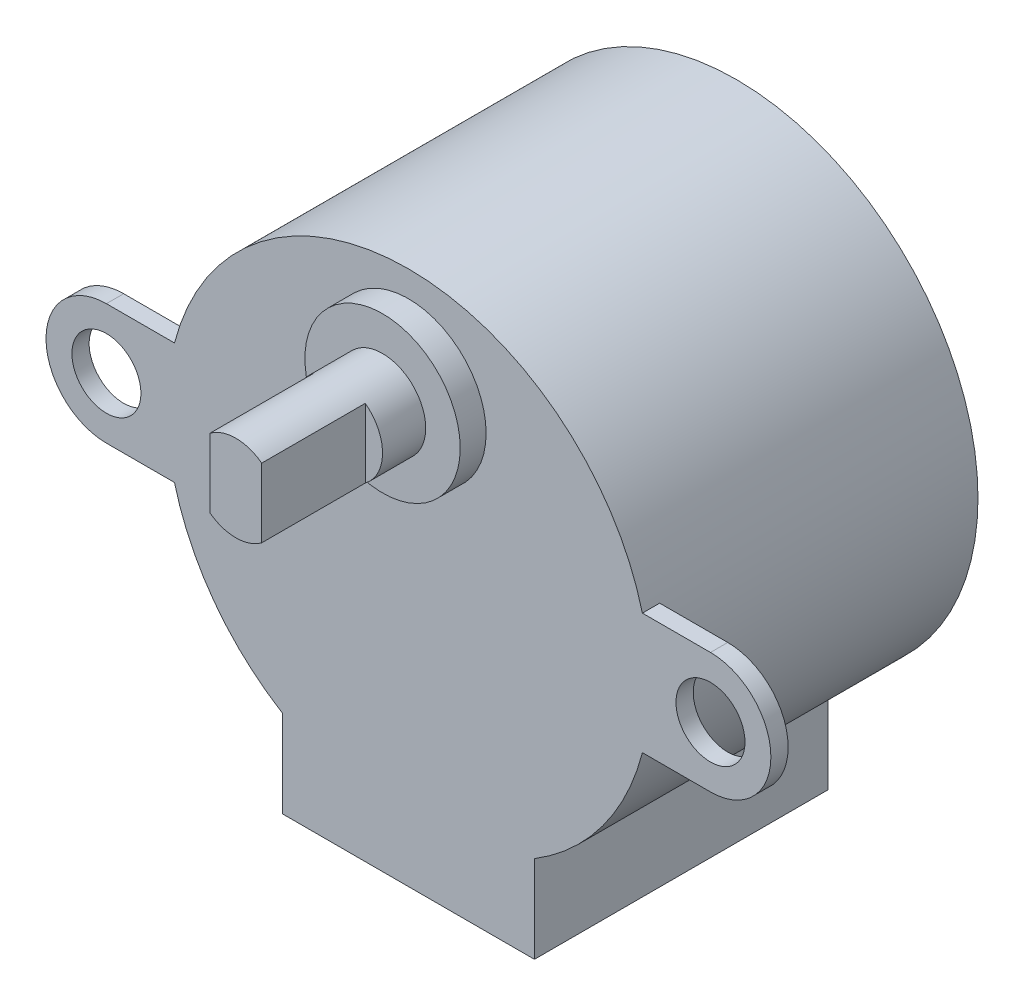
SolidWorks part; units mm, degrees
ref_plane "Front Plane" through (0, 0, 0) normal (0, 0, 1) x (1, 0, 0)
ref_plane "Top Plane" through (0, 0, 0) normal (0, 1, 0) x (1, 0, 0)
ref_plane "Right Plane" through (0, 0, 0) normal (1, 0, 0) x (0, 0, -1)
sketch "Sketch2" plane through (0, 0, 0) normal (0, 0, 1) x (1, 0, 0)
  circle A0 centre (0, 0) radius 14
  dimension "D1" = 28
extrude "Boss-Extrude2" add sketch "Sketch2" along normal blind 19
sketch "Sketch3" plane through (0, 0, 19) normal (0, 0, 1) x (1, 0, 0)
  circle A0 centre (0, 8) radius 4.5
  dimension "D1" = 9
  dimension "D2" = 8
extrude "Boss-Extrude3" add sketch "Sketch3" along normal blind 1.5
sketch "Sketch4" plane through (0, 0, 20.5) normal (0, 0, 1) x (1, 0, 0)
  circle A0 centre (0, 8) radius 2.5
  dimension "D1" = 5
extrude "Boss-Extrude4" add sketch "Sketch4" along normal blind 2.5
sketch "Sketch5" plane through (0, 0, 19) normal (0, 0, 1) x (1, 0, 0)
  line L0 (0, -18.6594) -> (0, 24.7724) construction
  line L1 (17.5, 3.5) -> (13.5554, 3.5)
  line L2 (17.5, -3.5) -> (13.5554, -3.5)
  line L3 (-17.5, -3.5) -> (-13.5554, -3.5)
  line L4 (-17.5, 3.5) -> (-13.5554, 3.5)
  circle A0 centre (17.5, 0) radius 2
  arc A1 (17.5, -3.5) -> (17.5, 3.5) centre (17.5, 0) ccw
  circle A2 centre (0, 0) radius 14 construction
  arc A3 (13.5554, -3.5) -> (13.5554, 3.5) centre (0, 0) ccw
  arc A4 (-13.5554, 3.5) -> (-13.5554, -3.5) centre (0, 0) ccw
  arc A5 (-13.5554, -3.5) -> (-13.5554, 3.5) centre (0, 0) cw
  arc A6 (-17.5, -3.5) -> (-17.5, 3.5) centre (-17.5, 0) cw
  circle A7 centre (-17.5, 0) radius 2
  circle M3 centre (0, 0) radius 14
  dimension "D1" = 4
  dimension "D2" = 7
  dimension "D3" = 17.5
extrude "Boss-Extrude5" add sketch "Sketch5" against normal blind 1 contours L2 A1 L1 A0 M3 | A6 L3 L4 A7 M3
sketch "Sketch6" plane through (0, 0, 19) normal (0, 0, 1) x (1, 0, 0)
  line L1 (-7.3, -17) -> (7.3, -17)
  line L2 (-7.3, -17) -> (-7.3, -7.7685)
  line L3 (-7.3, -7.7685) -> (7.3, -7.7685)
  line L4 (7.3, -17) -> (7.3, -7.7685)
  line L5 (-7.3, -17) -> (7.3, -7.7685) construction
  line L6 (-7.3, -7.7685) -> (7.3, -17) construction
  point P0 (0, -12.3843)
  dimension "D1" = 17
  dimension "D2" = 14.6
extrude "Boss-Extrude6" add sketch "Sketch6" against normal blind 17
sketch "Sketch7" plane through (0, 0, 23) normal (0, 0, 1) x (1, 0, 0)
  line L0 (-1.5, 6) -> (-1.5, 10)
  line L1 (1.5, 6) -> (1.5, 10)
  circle A1 centre (0, 8) radius 2.5 construction
  circle A2 centre (0, 8) radius 2.5 construction
  arc A3 (1.5, 10) -> (-1.5, 10) centre (0, 8) ccw
  circle A4 centre (0, 8) radius 2.5
  arc A5 (-1.5, 6) -> (1.5, 6) centre (0, 8) ccw
  dimension "D1" = 3
  dimension "D2" = 0
extrude "Boss-Extrude7" add sketch "Sketch7" along normal blind 6
